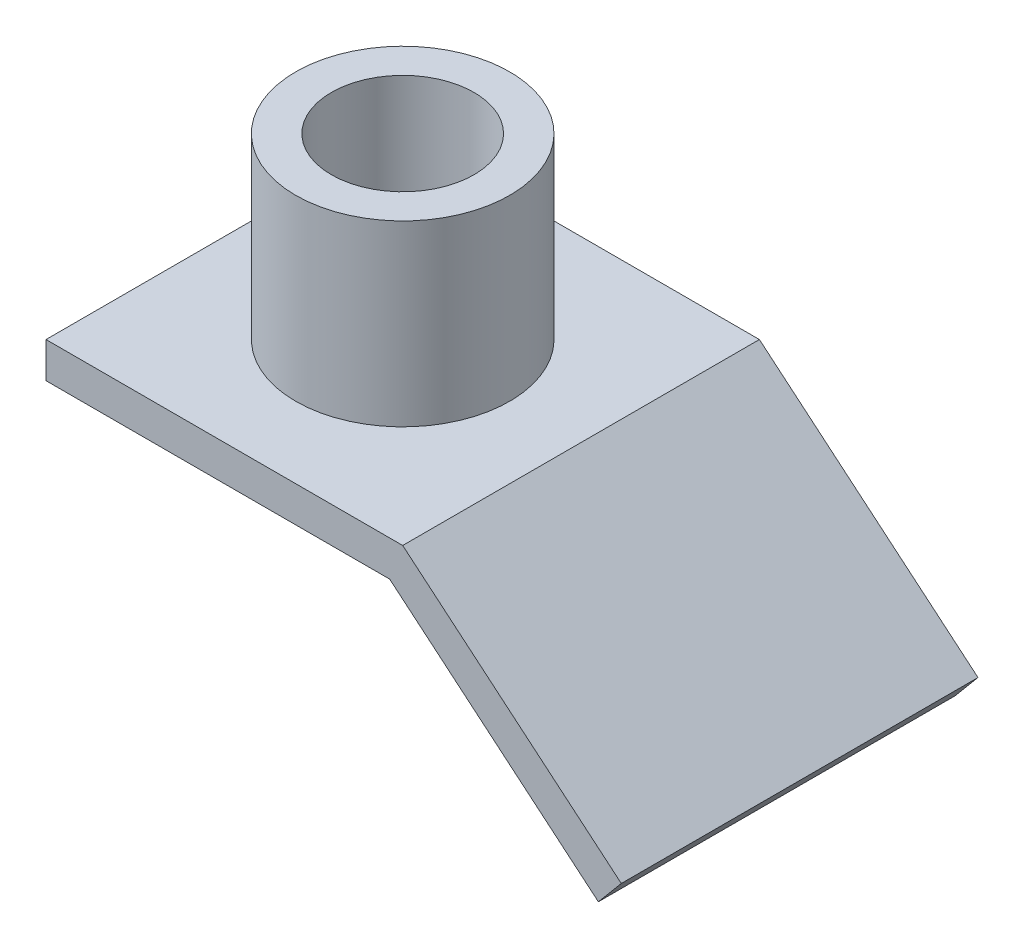
SolidWorks part; units mm, degrees
ref_plane "Front Plane" through (0, 0, 0) normal (0, 0, 1) x (1, 0, 0)
ref_plane "Top Plane" through (0, 0, 0) normal (0, 1, 0) x (1, 0, 0)
ref_plane "Right Plane" through (0, 0, 0) normal (1, 0, 0) x (0, 0, -1)
sketch "Sketch1" plane through (0, 0, 0) normal (0, 0, 1) x (1, 0, 0)
  line L0 (-128.4722, 0) -> (125.3495, 0) construction
  line L1 (0, 105.8116) -> (0, -93.0078) construction
  line L2 (-50, 0) -> (50, 0)
  line L3 (50, 0) -> (111.2836, -51.423)
  dimension "D1" = 100
  dimension "D2" = 50
  dimension "D3" = 140
  dimension "D4" = 80
extrude "Extrude-Thin1" add sketch "Sketch1" along normal mid plane 100 thin
sketch "Sketch3" plane through (0, 0, 0) normal (0, 1, 0) x (1, 0, 0)
  line L0 (0, 62.8414) -> (0, -66.9071) construction
  line L1 (-80.2808, 0) -> (132.3724, 0) construction
  circle A0 centre (0, 0) radius 30
  dimension "D1" = 60
extrude "Boss-Extrude1" add sketch "Sketch3" along normal blind 50
sketch "Sketch4" plane through (0, 50, 0) normal (0, 1, 0) x (1, 0, 0)
  circle A0 centre (0, 0) radius 20
  dimension "D1" = 40
extrude "Cut-Extrude1" cut sketch "Sketch4" against normal through all
